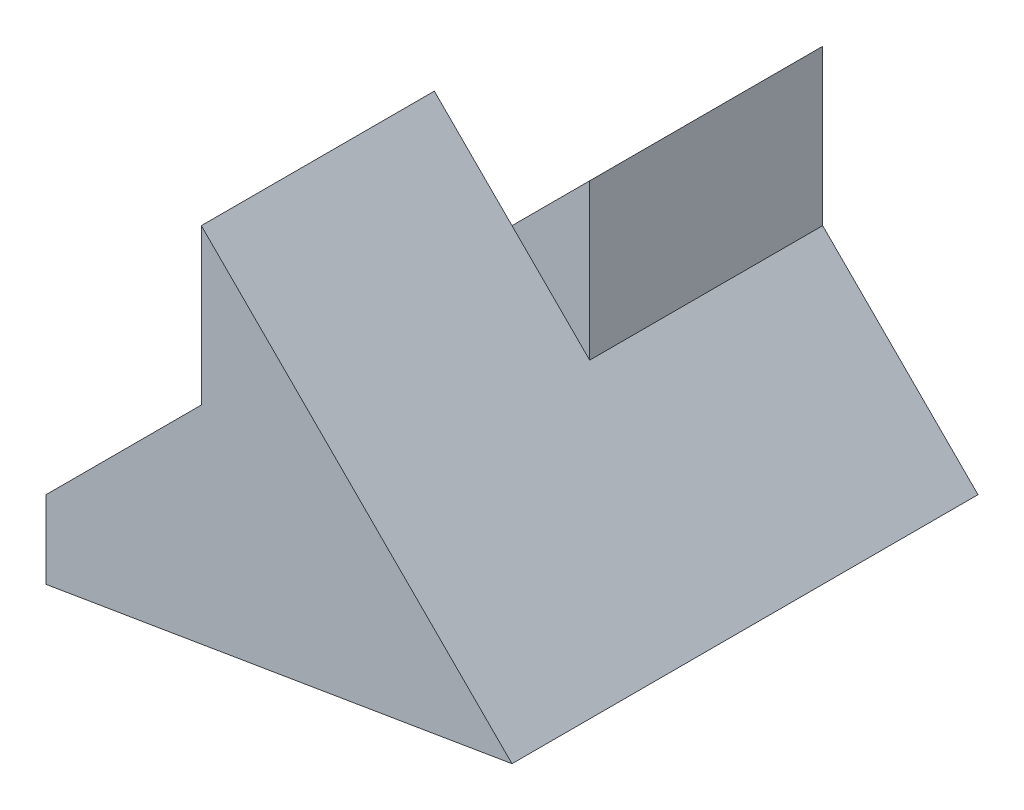
SolidWorks part; units mm, degrees
ref_plane "Front Plane" through (0, 0, 0) normal (0, 0, 1) x (1, 0, 0)
ref_plane "Top Plane" through (0, 0, 0) normal (0, 1, 0) x (1, 0, 0)
ref_plane "Right Plane" through (0, 0, 0) normal (1, 0, 0) x (0, 0, -1)
sketch "Sketch2" plane through (0, 0, 0) normal (0, 0, 1) x (1, 0, 0)
  line L0 (0, 0) -> (6, 1)
  line L1 (6, 1) -> (2, 5)
  line L2 (2, 5) -> (2, 3)
  line L3 (2, 3) -> (0, 1)
  line L4 (0, 1) -> (0, 0)
  dimension "D1" = 1
  dimension "D2" = 6
  dimension "D3" = 4
  dimension "D4" = 4
  dimension "D5" = 2
  dimension "D6" = 2
extrude "Boss-Extrude1" add sketch "Sketch2" along normal blind 3
sketch "Sketch3" plane through (0, 0, 0) normal (0, 0, -1) x (-1, 0, 0)
  line L0 (0, 0) -> (0, 1)
  line L1 (0, 0) -> (-6, 1)
  line L2 (-6, 1) -> (-4, 3)
  line L3 (-6, 1) -> (-2, 5) construction
  line L4 (-4, 3) -> (-4, 5)
  line L5 (0, 1) -> (-4, 5)
  dimension "D1" = 4
  dimension "D2" = 4
extrude "Boss-Extrude2" add sketch "Sketch3" along normal blind 3
